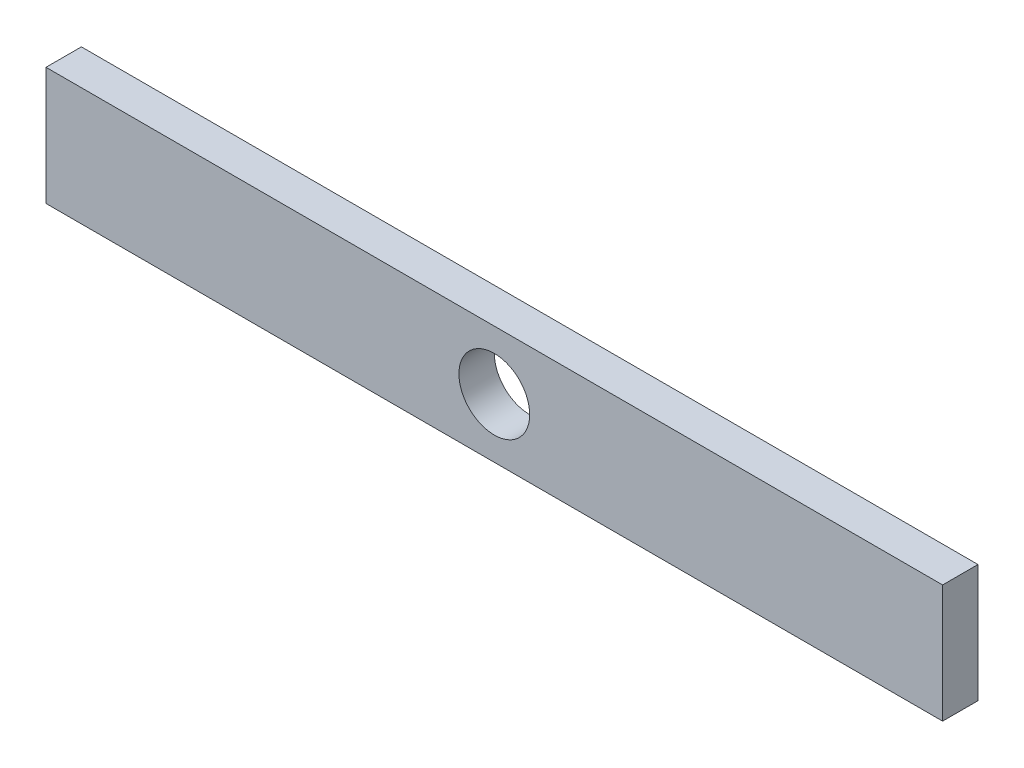
SolidWorks part; units mm, degrees
ref_plane "Front Plane" through (0, 0, 0) normal (0, 0, 1) x (1, 0, 0)
ref_plane "Top Plane" through (0, 0, 0) normal (0, 1, 0) x (1, 0, 0)
ref_plane "Right Plane" through (0, 0, 0) normal (1, 0, 0) x (0, 0, -1)
sketch "Sketch1" plane through (0, 0, 0) normal (0, 0, 1) x (1, 0, 0)
  line L1 (-30.2275, 10) -> (45.7725, 10)
  line L2 (-30.2275, 10) -> (-30.2275, 0)
  line L3 (-30.2275, 0) -> (45.7725, 0)
  line L4 (45.7725, 10) -> (45.7725, 0)
  circle A0 centre (7.7725, 5) radius 3
extrude "Boss-Extrude2" add sketch "Sketch1" along normal blind 3
